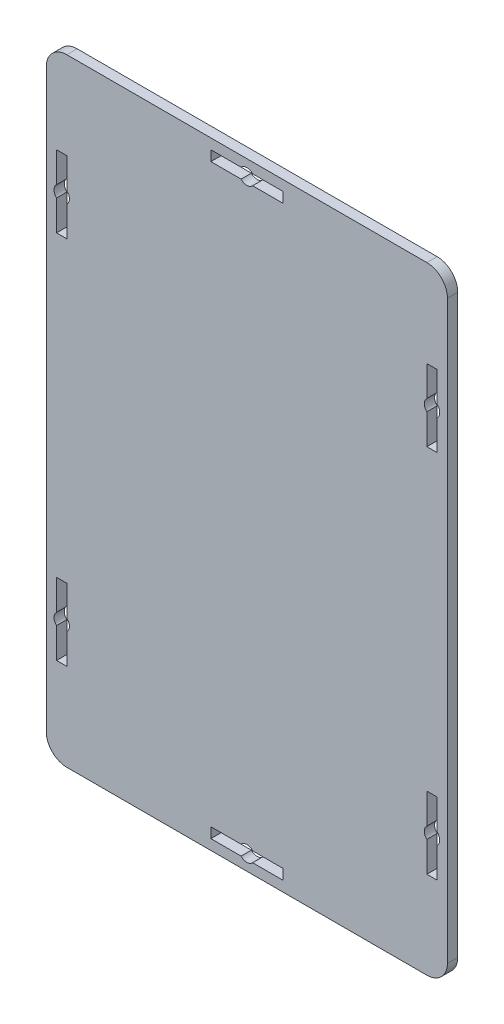
SolidWorks part; units mm, degrees
material "Acrylic (Medium-high impact)"
ref_plane "Front Plane" through (0, 0, 0) normal (0, 0, 1) x (1, 0, 0)
ref_plane "Top Plane" through (0, 0, 0) normal (0, 1, 0) x (1, 0, 0)
ref_plane "Right Plane" through (0, 0, 0) normal (1, 0, 0) x (0, 0, -1)
sketch "Sketch1" plane through (0, 0, 0) normal (0, 0, 1) x (1, 0, 0)
  line L0 (40.118, 4) -> (46, 4)
  line L1 (0, 0) -> (78, 0)
  line L2 (0, 0) -> (0, 120)
  line L3 (0, 120) -> (78, 120)
  line L4 (78, 0) -> (78, 120)
  line L5 (40.118, 2) -> (46, 2)
  line L6 (40.118, 118) -> (46, 118)
  line L7 (40.118, 116) -> (46, 116)
  line L8 (74, 97.118) -> (74, 103)
  line L9 (76, 97.118) -> (76, 103)
  line L10 (4, 97.118) -> (4, 103)
  line L11 (2, 97.118) -> (2, 103)
  line L12 (2, 22.882) -> (2, 17)
  line L13 (4, 22.882) -> (4, 17)
  line L14 (0, 60) -> (78, 60) construction
  line L15 (74, 22.882) -> (74, 17)
  line L16 (76, 22.882) -> (76, 17)
  line L23 (32, 118) -> (37.882, 118)
  line L24 (32, 118) -> (32, 116)
  line L25 (32, 116) -> (37.882, 116)
  line L26 (46, 118) -> (46, 116)
  line L27 (32, 118) -> (46, 116) construction
  line L28 (32, 116) -> (46, 118) construction
  line L29 (39, 60) -> (39, 120) construction
  line L30 (32, 4) -> (46, 2) construction
  line L31 (32, 2) -> (46, 4) construction
  line L32 (46, 2) -> (46, 4)
  line L33 (32, 4) -> (37.882, 4)
  line L34 (32, 2) -> (32, 4)
  line L35 (32, 2) -> (37.882, 2)
  line L37 (39, 60) -> (39, 0) construction
  line L38 (2, 31) -> (4, 31)
  line L39 (2, 31) -> (2, 25.118)
  line L40 (2, 17) -> (4, 17)
  line L41 (4, 31) -> (4, 25.118)
  line L42 (2, 31) -> (4, 17) construction
  line L43 (2, 17) -> (4, 31) construction
  line L44 (76, 17) -> (74, 31) construction
  line L45 (76, 31) -> (74, 17) construction
  line L46 (74, 31) -> (74, 25.118)
  line L47 (76, 17) -> (74, 17)
  line L48 (76, 31) -> (76, 25.118)
  line L49 (76, 31) -> (74, 31)
  line L50 (76, 89) -> (74, 103) construction
  line L51 (76, 103) -> (74, 89) construction
  line L52 (76, 89) -> (74, 89)
  line L53 (76, 89) -> (76, 94.882)
  line L54 (76, 103) -> (74, 103)
  line L55 (74, 89) -> (74, 94.882)
  line L56 (2, 103) -> (4, 89) construction
  line L57 (2, 89) -> (4, 103) construction
  line L58 (4, 89) -> (4, 94.882)
  line L59 (2, 103) -> (4, 103)
  line L60 (2, 89) -> (2, 94.882)
  line L61 (2, 89) -> (4, 89)
  arc A0 (2, 97.118) -> (2, 94.882) centre (3, 96) ccw
  arc A1 (74, 97.118) -> (74, 94.882) centre (75, 96) ccw
  arc A2 (4, 22.882) -> (4, 25.118) centre (3, 24) ccw
  arc A3 (74, 25.118) -> (74, 22.882) centre (75, 24) ccw
  arc A4 (37.882, 2) -> (40.118, 2) centre (39, 3) ccw
  arc A5 (37.882, 116) -> (40.118, 116) centre (39, 117) ccw
  arc A6 (40.118, 4) -> (37.882, 4) centre (39, 3) ccw
  arc A7 (40.118, 118) -> (37.882, 118) centre (39, 117) ccw
  arc A8 (76, 94.882) -> (76, 97.118) centre (75, 96) ccw
  arc A9 (4, 94.882) -> (4, 97.118) centre (3, 96) ccw
  arc A10 (2, 25.118) -> (2, 22.882) centre (3, 24) ccw
  arc A11 (76, 22.882) -> (76, 25.118) centre (75, 24) ccw
  point P45 (39, 117)
  point P58 (39, 3)
  point P59 (3, 24)
  point P69 (75, 24)
  point P74 (75, 96)
  point P79 (3, 96)
  dimension "D4" = 3
  dimension "D2" = 24
  dimension "D3" = 78
  dimension "D5" = 14
  dimension "D6" = 120
  dimension "D16" = 2
  dimension "D17" = 2
  dimension "D18" = 14
  dimension "D19" = 2
extrude "Main Slider Bottom" add sketch "Sketch1" along normal blind 2
fillet "Slider Bottom Contouring" radius 4 4 edges at (0, 0, 1) (78, 0, 1) (78, 120, 1) (0, 120, 1)
